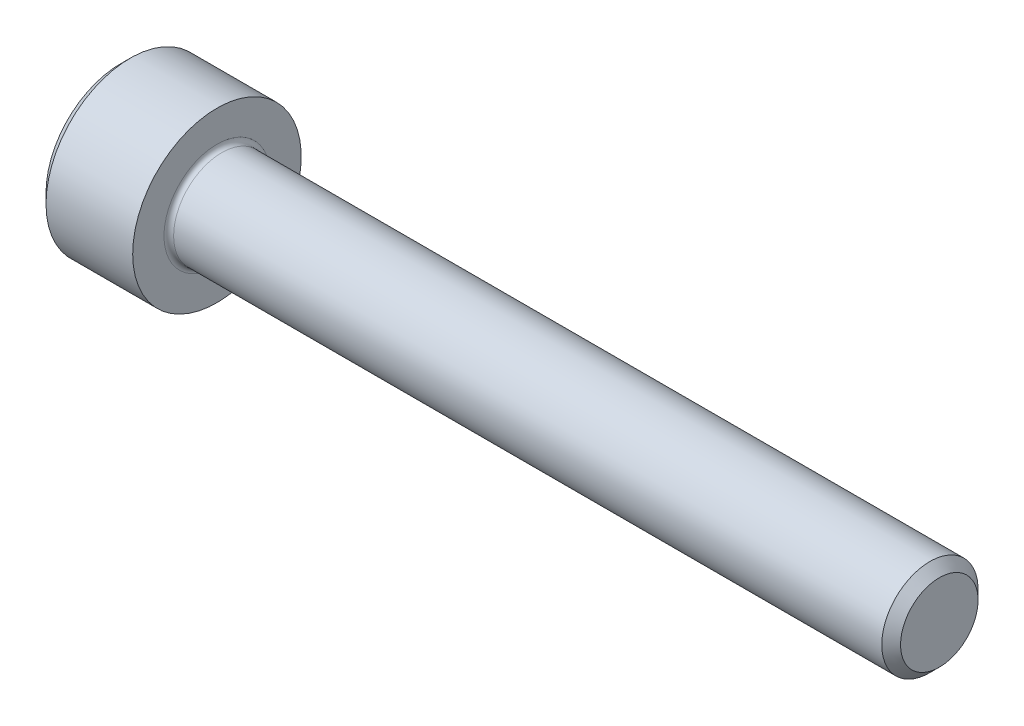
SolidWorks part; units mm, degrees
revolve "Base-Revolve" add sketch "BodySke"
sketch "BodySke" plane through (0, 0, 0) normal (0, 0, 1) x (1, 0, 0)
  line L0 (0, 0) -> (0, 3.1)
  line L1 (0.4, 3.5) -> (4, 3.5)
  line L2 (4, 3.5) -> (4, 2)
  line L3 (4, 2) -> (33.61, 2)
  line L4 (34, 1.61) -> (34, 0)
  line L5 (34, 0) -> (0, 0)
  line L6 (-31.75, 0) -> (127, 0) construction
  line L7 (0, 3.1) -> (0.4, 3.5)
  line L8 (34, 1.61) -> (33.61, 2)
  line L9 (0, -3.1) -> (0.4, -3.5) construction
  line L10 (34, -1.61) -> (33.61, -2) construction
  line L11 (4.7, 9.525) -> (4.7, 3.175) construction
  line L12 (14, 9.525) -> (14, 3.175) construction
  line L13 (-16, 9.525) -> (-16, 3.175) construction
  dimension "Diameter" = 4
  dimension "Head_ht" = 4
  dimension "Length" = 30
  dimension "Body_ch_ang" = 45
  dimension "Head_dia" = 7
  dimension "Head_ch_ang" = 45
  dimension "Minor_dia" = 3.22
  dimension "Advance" = 0.7
  dimension "Thread_nom" = 20
  dimension "Thread_length" = 50
  dimension "Head_ch_ht" = 0.4
cosmetic thread "ThreadCosmetic" [suppressed]
fillet "Fillet1" radius 0.2 1 edges at (4, 0, 2)
ref_plane "Plane1" through (0, 0, 0) normal (0, 0, 1) x (1, 0, 0)
ref_plane "Plane2" through (0, 0, 0) normal (0, 1, 0) x (1, 0, 0)
ref_plane "Plane3" through (0, 0, 0) normal (1, 0, 0) x (0, 0, -1)
other "Configuration Table"
sketch "Sketch2" plane through (0, 0, 0) normal (0, 0, 1) x (1, 0, 0)
  line L0 (0, 1.5355) -> (2, 1.5355)
  line L1 (2, 1.5355) -> (2.8865, 0)
  line L2 (-31.75, 0) -> (127, 0) construction
  line L3 (2.8865, 0) -> (0, 0)
  line L4 (0, 0) -> (0, 1.5355)
  line L5 (0, 3.1) -> (0, -3.1) construction
  line L6 (0, 0) -> (47.625, 0) construction
  line L7 (4, -3.5) -> (4, 3.5) construction
  dimension "D1" = 1.5355
  dimension "D2" = 60
revolve "Hex-PreBroach" cut sketch "Sketch2" angle 360 about L6
sketch "Sketch3" plane through (0, 0, 0) normal (-1, 0, 0) x (0, 0.5, 0.866)
  line L0 (0.8865, 1.5355) -> (-0.8865, 1.5355)
  line L1 (-0.8865, 1.5355) -> (-1.773, 0)
  line L2 (0.8865, 1.5355) -> (1.773, 0)
  line L3 (0.8865, -1.5355) -> (1.773, 0)
  line L4 (0.8865, -1.5355) -> (-0.8865, -1.5355)
  line L5 (-0.8865, -1.5355) -> (-1.773, 0)
  dimension "D1" = 1.5355
  dimension "D2" = 1.5355
  dimension "Hex_size" = 3.071
extrude "Hex" cut sketch "Sketch3" against normal blind 2
sketch "Sketch4" plane through (0, 0, 0) normal (-1, 0, 0) x (0, 0, 1)
  line L0 (0, 0) -> (1.7399, 0)
  line L1 (0, 0) -> (6.1484, 3.5498) construction
  line L2 (0, 0) -> (0.8699, 1.5068)
  line L3 (1.4457, 0.3947) -> (1.6607, 0.5189)
  line L4 (1.0647, 1.0546) -> (1.2797, 1.1788)
  arc A0 (1.4457, 0.3947) -> (1.0647, 1.0546) centre (0, 0) ccw
  arc A1 (1.7399, 0) -> (1.6607, 0.5189) centre (0, 0) ccw
  arc A2 (0.8699, 1.5068) -> (1.2797, 1.1788) centre (0, 0) cw
  dimension "D1" = 30
  dimension "D2" = 60
  dimension "Spline_p_dim" = 0.762
  dimension "D3" = 0.381
extrude "Spline" [suppressed] cut sketch "Sketch4" against normal blind 2
pattern_circular "CirPattern1" [suppressed] count 6 every 60
sketch "Sketch5" plane through (0, 0, 0) normal (0, 0, 1) x (1, 0, 0)
  line L0 (-31.75, 0) -> (127, 0) construction
  line L2 (0, 3.1) -> (0, -3.1) construction
  circle A0 centre (1.6, 0) radius 0.675
  dimension "Drilled_hole_dia" = 1.35
  dimension "Drilled_hole_loc" = 1.6
extrude "Hole" [suppressed] cut sketch "Sketch5" against normal through all and the other way through all
pattern_circular "Drilled-4" [suppressed] count 2 every 60
pattern_circular "Drilled-6" [suppressed] count 3 every 60
sketch "ThdSchSke" plane through (0, 0, 0) normal (0, 0, 1) x (1, 0, 0)
  line L0 (14, -1.61) -> (13.7269, -2)
  line L1 (14, -1.61) -> (14.2731, -2)
  line L2 (14.2731, -2) -> (14.2731, -2.5)
  line L3 (-3.175, 0) -> (5.1513, 0) construction
  line L5 (14.2731, -2.5) -> (13.7269, -2.5)
  line L6 (13.7269, -2.5) -> (13.7269, -2)
  line L7 (0, 3.1) -> (0, -3.1) construction
  dimension "Thread_minor" = 3.22
  dimension "Diameter" = 4
  dimension "Start" = 14
revolve "ThreadSchematic" [suppressed] cut sketch "ThdSchSke" angle 360 about L3
pattern_linear "ThdSchPat" [suppressed]
equation "\"D2@Sketch3\" = \"Hex_size@Sketch3\" / 2"
equation "\"D1@Sketch3\" = \"Hex_size@Sketch3\" / 2"
equation "\"D1@Sketch2\" = \"Hex_size@Sketch3\" / 2"
equation "\"D3@Sketch4\" = \"Spline_p_dim@Sketch4\" / 2"
equation "\"Thread_minor@ThreadCosmetic\"  =  \"Minor_dia@BodySke\""
equation "\"D2@CirPattern1\" = 360 / \"Num_teeth@CirPattern1\""
equation "\"Wall_thickness@Sketch2\" = \"Head_ht@BodySke\" - \"Key_eng@Hex\""
equation "\"Thread_length@ThreadCosmetic\" = ((sgn( (\"Length@BodySke\" - \"Advance@BodySke\" ) - \"Thread_nom@BodySke\" )-1)*( (\"Length@BodySke\" - \"Advance@BodySke\" ) - \"Thread_nom@BodySke\" ))/-2+ \"Thread_nom@BodySke\""
equation "\"Thread_minor@ThdSchSke\" = \"Minor_dia@BodySke\""
equation "\"Diameter@ThdSchSke\" = \"Diameter@BodySke\""
equation "\"Overcut@ThdSchSke\" = \"Diameter@BodySke\" * 1.25"
equation "\"Start@ThdSchSke\" = \"Head_ht@BodySke\" + \"Length@BodySke\" - \"Thread_length@ThreadCosmetic\"  '---Non-countersunk---"
equation "\"Num_threads@ThdSchPat\" = int( \"Thread_length@ThreadCosmetic\" / \"Advance@BodySke\" + 0.999 )  + 1"
equation "\"Advance@ThdSchPat\" = \"Thread_length@ThreadCosmetic\" /  (\"Num_threads@ThdSchPat\" - 1) 'relax it"
equation "\"Num_threads@ThdSchPat\" = \"Num_threads@ThdSchPat\" - sgn( \"Num_threads@ThdSchPat\" - 1) '---chamfered tips only---"
